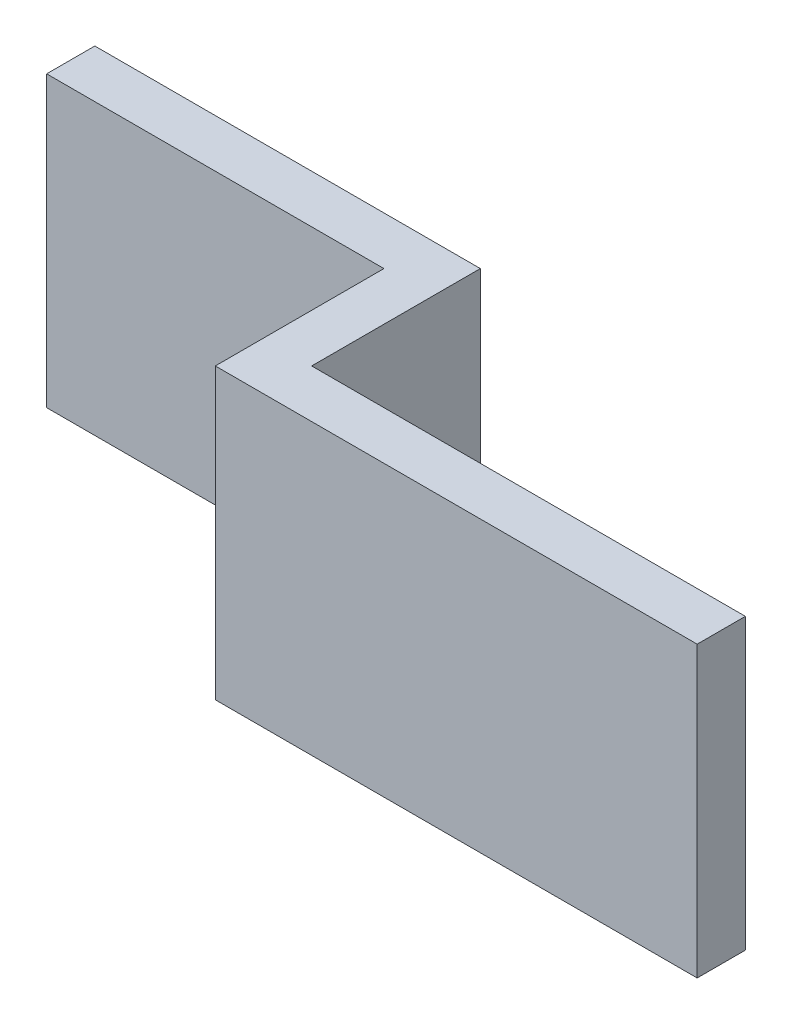
SolidWorks part; units mm, degrees
ref_plane "Front Plane" through (0, 0, 0) normal (0, 0, 1) x (1, 0, 0)
ref_plane "Top Plane" through (0, 0, 0) normal (0, 1, 0) x (1, 0, 0)
ref_plane "Right Plane" through (0, 0, 0) normal (1, 0, 0) x (0, 0, -1)
sketch "Sketch1" plane through (0, 0, 0) normal (0, 1, 0) x (1, 0, 0)
  line L0 (0, 0.5) -> (1, 0.5)
  line L1 (0, -4) -> (10, -4)
  line L2 (0, -4) -> (0, 0.5)
  line L4 (10, -4) -> (10, -3)
  line L5 (0, 0.5) -> (-7, 0.5)
  line L6 (0, 0.5) -> (0, -0.5)
  line L7 (0, -0.5) -> (-7, -0.5)
  line L8 (-7, 0.5) -> (-7, -0.5)
  line L9 (-3.5, -0.5) -> (-3.5, 0.5) construction
  line L10 (0, 0) -> (-7, 0) construction
  line L11 (1, 0.5) -> (1, -3)
  line L12 (1, -3) -> (10, -3)
  point P1 (0, 0)
  point P85 (-3.5, 0)
  dimension "D1" = 17
  dimension "D2" = 1
  dimension "D3" = 10
  dimension "D5" = 4
extrude "Boss-Extrude1" add sketch "Sketch1" along normal mid plane 6
sketch "Sketch2" plane through (0, 3, 0) normal (0, 1, 0) x (1, 0, 0)
  line L1 (0, 4) -> (10, 4)
  line L2 (0, 4) -> (0, -4)
  line L3 (0, -4) -> (10, -4)
  line L4 (10, 4) -> (10, -4)
  line L5 (5, -4) -> (5, 4) construction
  line L6 (0, 0) -> (10, 0) construction
  point P108 (5, 0)
extrude "Boss-Extrude2" [suppressed] add sketch "Sketch2" along normal blind 3
